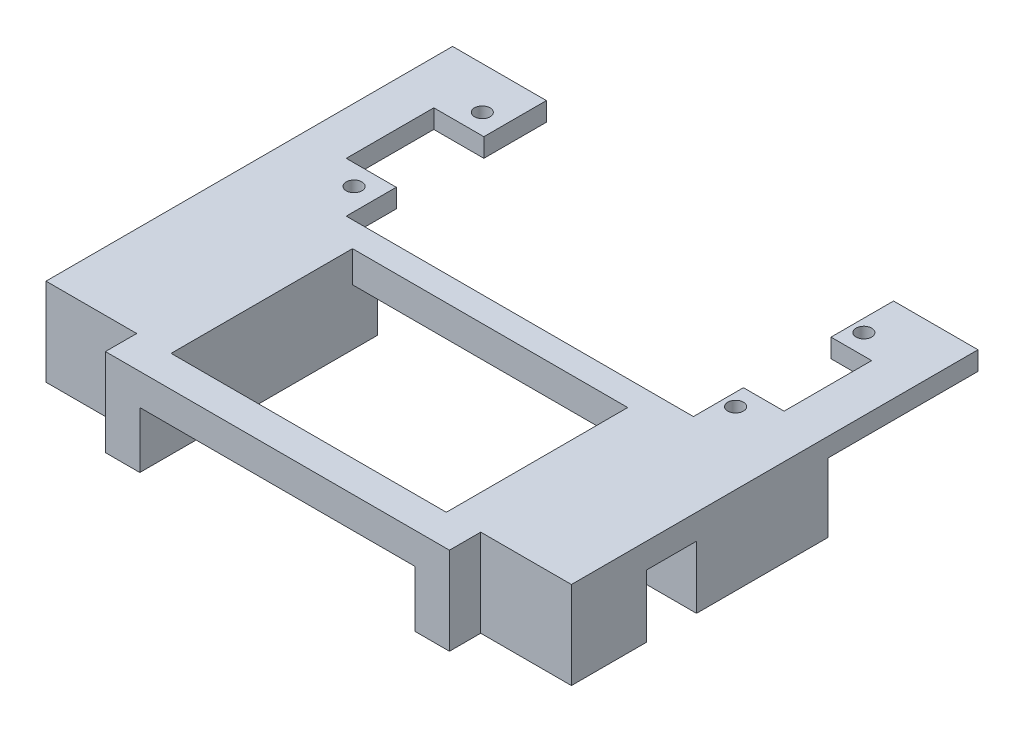
SolidWorks part; units mm, degrees
ref_plane "Front Plane" through (0, 0, 0) normal (0, 0, 1) x (1, 0, 0)
ref_plane "Top Plane" through (0, 0, 0) normal (0, 1, 0) x (1, 0, 0)
ref_plane "Right Plane" through (0, 0, 0) normal (1, 0, 0) x (0, 0, -1)
sketch "Sketch1" plane through (0, 0, 0) normal (0, 1, 0) x (1, 0, 0)
  line L0 (0, 0) -> (0, 31.2652) construction
  line L1 (-29.5, -11) -> (29.5, -11)
  line L5 (-42, -60) -> (42, -60) construction
  line L6 (65.83, -60) -> (108.3156, -60) construction
  line L8 (-42, -11) -> (42, -11)
  line L11 (-5.25, -11) -> (5.25, -11)
  line L13 (-35, -13) -> (35, -13)
  line L14 (-35, -13) -> (-35, -43)
  line L15 (-42, -76) -> (42, -76)
  line L16 (-115.1518, -60) -> (-65.222, -60) construction
  line L21 (42, -11) -> (42, -76)
  line L22 (-42, -11) -> (-42, -76)
  line L23 (-35, -43) -> (35, -43)
  line L28 (-22, -47) -> (22, -47)
  line L29 (-22, -47) -> (-22, -76)
  line L30 (-22, -76) -> (22, -76)
  line L31 (22, -47) -> (22, -76)
  line L32 (-22, -47) -> (22, -76) construction
  line L33 (-22, -76) -> (22, -47) construction
  line L34 (-27.5, -76) -> (27.5, -76)
  line L35 (-27.5, -76) -> (-27.5, -81)
  line L36 (-27.5, -81) -> (27.5, -81)
  line L37 (27.5, -76) -> (27.5, -81)
  line L38 (-27.5, -76) -> (27.5, -81) construction
  line L39 (-27.5, -81) -> (27.5, -76) construction
  line L40 (35, -13) -> (35, -43)
  line L41 (-35, -13) -> (35, -43) construction
  line L42 (-35, -43) -> (35, -13) construction
  point P9 (0, -28)
  point P13 (0, 0)
  point P20 (0, -11)
  point P30 (0, -78.5)
  point P40 (0, -61.5)
  dimension "D2" = 11
  dimension "D9" = 5
  dimension "D10" = 55
  dimension "D3" = 84
  dimension "D4" = 30
  dimension "D5" = 2
  dimension "D6" = 70
  dimension "D7" = 42
  dimension "D8" = 65
  dimension "D13" = 16
  dimension "D14" = 44
  dimension "D15" = 29
extrude "Boss-Extrude1" add sketch "Sketch1" along normal blind 5
sketch "Sketch2" plane through (0, 0, 0) normal (0, -1, 0) x (1, 0, 0)
  line L0 (0, 0) -> (0, 96.1896) construction
  line L1 (-42, 76) -> (-22, 76)
  line L2 (-42, 76) -> (-42, 43)
  line L3 (-42, 43) -> (-22, 43)
  line L4 (-22, 76) -> (-22, 43)
  line L5 (-42, 76) -> (-22, 43) construction
  line L6 (-42, 43) -> (-22, 76) construction
  line L7 (-42, 76) -> (-27.5, 76) construction
  line L8 (-42, 11) -> (-42, 76) construction
  line L9 (27.5, 76) -> (27.5, 81) construction
  line L10 (22, 76) -> (27.5, 76)
  line L11 (42, 43) -> (22, 43)
  line L12 (22, 76) -> (22, 43)
  line L13 (42, 76) -> (22, 76)
  line L14 (42, 76) -> (42, 43)
  line L15 (-35, 43) -> (35, 43) construction
  line L16 (-42, 11) -> (-42, 76) construction
  line L17 (-42, 43) -> (-35, 43)
  line L18 (-42, 43) -> (-42, 35)
  line L19 (-42, 35) -> (-35, 35)
  line L20 (-35, 43) -> (-35, 35)
  line L21 (-42, 43) -> (-35, 35) construction
  line L22 (-42, 35) -> (-35, 43) construction
  line L23 (42, 35) -> (35, 35)
  line L24 (-22, 47) -> (-22, 76) construction
  line L25 (22, 76) -> (22, 81)
  line L26 (22, 81) -> (27.5, 81)
  line L27 (27.5, 76) -> (27.5, 81)
  line L28 (22, 76) -> (27.5, 81) construction
  line L29 (22, 81) -> (27.5, 76) construction
  line L30 (-27.5, 81) -> (27.5, 81) construction
  line L31 (-22, 76) -> (22, 76) construction
  line L32 (-22, 81) -> (-27.5, 81)
  line L33 (-27.5, 76) -> (-27.5, 81)
  line L34 (-22, 76) -> (-27.5, 76)
  line L35 (-22, 76) -> (-22, 81)
  line L36 (35, 43) -> (35, 35)
  line L37 (42, 43) -> (35, 43)
  line L38 (42, 43) -> (42, 35)
  point P0 (-32, 59.5)
  point P21 (-38.5, 39)
  point P29 (24.75, 78.5)
  point P43 (0, 12)
  line M5 (42, 76) -> (27.5, 76)
  line M9 (-27.5, 76) -> (-42, 76)
  line M10 (-42, 76) -> (-42, 11)
  line M12 (42, 11) -> (42, 76)
  line M14 (-22, 47) -> (-22, 76)
  line M16 (22, 76) -> (22, 47)
  line M18 (-35, 13) -> (-35, 43)
  line M19 (-35, 43) -> (35, 43)
  dimension "D1" = 8
  dimension "D2" = 7
extrude "Boss-Extrude2" add sketch "Sketch2" along normal blind 9 contours L12 L11 L10 M16 M19 M12 M5 | L4 L1 L3 M14 M9 M10 M19 | L19 L3 M10 M18
sketch "Sketch3" plane through (0, 0, 0) normal (0, -1, 0) x (1, 0, 0)
  line L13 (-42, 35) -> (-42, 11)
  line L15 (42, 35) -> (35, 35)
  line L21 (-42, 35) -> (-42, 11)
  line L27 (-35, 13) -> (-35, 35)
  line L29 (-35, 13) -> (-35, 35)
  line L32 (35, 35) -> (35, 13)
  line L35 (35, 35) -> (35, 13)
  line L37 (-35, 35) -> (-42, 35)
  line L38 (-35, 35) -> (-42, 35)
  line L39 (35, 13) -> (-35, 13)
  line L40 (35, 13) -> (-35, 13)
  line L41 (-42, 11) -> (42, 11)
  line L42 (-42, 11) -> (42, 11)
  line L43 (42, 11) -> (42, 35)
  line L44 (42, 11) -> (42, 35)
  line L45 (42, 35) -> (35, 35)
  dimension "D1" = 0
extrude "Cut-Extrude1" cut sketch "Sketch3" against normal blind 2
sketch "Sketch4" plane through (0, 5, 0) normal (0, 1, 0) x (1, 0, 0)
  line L0 (0, 0) -> (0, -72.3692) construction
  line L1 (-42, -11) -> (42, -11) construction
  circle A0 centre (-28, -46) radius 1.65
  circle A2 centre (28, -46) radius 1.65
  dimension "D3" = 3.3
  dimension "D1" = 28
  dimension "D2" = 35
extrude "Cut-Extrude2" [suppressed] cut sketch "Sketch4" against normal up to surface (14 mm away)
sketch "Sketch5" [suppressed] plane through (0, 5, 0) normal (0, 1, 0) x (1, 0, 0)
  line L0 (0, 0) -> (0, 24.796) construction
  circle A0 centre (28, -46) radius 1.65 construction
  circle A1 centre (-28, -46) radius 1.65 construction
  circle A2 centre (28, -46) radius 1.65
  circle A3 centre (-28, -46) radius 1.65
  circle A4 centre (-28, -46) radius 2.75
  circle A5 centre (28, -46) radius 2.75
  dimension "D1" = 5.5
extrude "Cut-Extrude3" [suppressed] cut sketch "Sketch5" against normal blind 10
sketch "Sketch6" plane through (0, 5, 0) normal (0, 1, 0) x (1, 0, 0)
  line L0 (0, -28) -> (0, 0) construction
  line L1 (-30.5, -17.75) -> (30.5, -17.75)
  line L2 (-30.5, -17.75) -> (-30.5, -38.25)
  line L3 (-30.5, -38.25) -> (30.5, -38.25)
  line L4 (30.5, -17.75) -> (30.5, -38.25)
  line L5 (-30.5, -17.75) -> (30.5, -38.25) construction
  line L6 (-30.5, -38.25) -> (30.5, -17.75) construction
  line L7 (0, -28) -> (-35, -28) construction
  line L8 (-35, -13) -> (-35, -43) construction
  line L9 (27, -13) -> (27, -21)
  line L10 (-35, -13) -> (35, -13) construction
  line L11 (27, -21) -> (35, -21)
  line L12 (35, -13) -> (35, -43) construction
  line L14 (-27, -13) -> (-27, -21)
  line L15 (-27, -21) -> (-35, -21)
  line L16 (27, -43) -> (27, -35)
  line L17 (27, -35) -> (35, -35)
  line L18 (-27, -43) -> (-27, -35)
  line L19 (-27, -35) -> (-35, -35)
  line L20 (-35, -43) -> (35, -43) construction
  line L21 (-35, -13) -> (-35, -43)
  line L22 (-35, -13) -> (35, -13)
  line L23 (35, -13) -> (35, -43)
  line L24 (-35, -43) -> (35, -43)
  circle A0 centre (-30.5, -17.75) radius 1.25
  circle A1 centre (30.5, -17.75) radius 1.25
  circle A2 centre (30.5, -38.25) radius 1.25
  circle A3 centre (-30.5, -38.25) radius 1.25
  point P0 (0, -28)
  line M17 (-35, -13) -> (35, -13)
  line M18 (35, -13) -> (35, -43)
  line M19 (35, -43) -> (-35, -43)
  line M20 (-35, -43) -> (-35, -13)
  dimension "D3" = 2.5
  dimension "D1" = 10.25
  dimension "D2" = 30.5
  dimension "D4" = 8
  dimension "D5" = 8
extrude "Boss-Extrude3" add sketch "Sketch6" against normal blind 3 contours A0 L1 L14 L15 L2 M17 M20 | A0 L2 L15 L14 L1 | L3 A3 L2 L19 L18 M20 M19 | L2 A3 L3 L18 L19 | A2 L3 L16 L17 L4 M19 M18 | A2 L4 L17 L16 L3 | L1 A1 L4 L11 L9 M18 M17 | L4 A1 L1 L9 L11
sketch "Sketch7" plane through (0, 5, 0) normal (0, 1, 0) x (1, 0, 0)
  line L0 (-27, -13) -> (-27, -11)
  line L1 (-42, -11) -> (42, -11) construction
  line L2 (27, -13) -> (27, -11)
  line L3 (-27, -13) -> (27, -13) construction
  line L4 (-27, -13) -> (27, -13)
  line L5 (27, -13) -> (27, -21) construction
  line L6 (27, -13) -> (27, -21)
  line L7 (28.5, -11) -> (28.5, -21)
  line L8 (27, -21) -> (35, -21) construction
  line L9 (-42, -11) -> (42, -11)
  line L10 (27, -21) -> (35, -21)
  line L11 (27.5, -81) -> (27.5, -76)
  line L12 (27.5, -76) -> (42, -76)
  line L13 (42, -76) -> (42, -11)
  line L14 (42, -11) -> (-42, -11)
  line L15 (-42, -11) -> (-42, -76)
  line L16 (-42, -76) -> (-27.5, -76)
  line L17 (-27.5, -76) -> (-27.5, -81)
  line L18 (-27.5, -81) -> (27.5, -81)
  line L22 (27, -11) -> (-27, -11)
  line L27 (27, -35) -> (28.5, -35)
  line L28 (28.5, -35) -> (28.5, -43)
  line L29 (28.5, -43) -> (27, -43)
  line L30 (27, -43) -> (27, -35)
  line L31 (27, -35) -> (35, -35) construction
  line L32 (-27, -43) -> (27, -43) construction
  line M15 (-27, -13) -> (27, -13)
  line M16 (27, -13) -> (27, -21)
  line M17 (27, -21) -> (35, -21)
  line M24 (42, -11) -> (-42, -11)
  dimension "D2" = 1.5
  dimension "D1" = 0
extrude "Cut-Extrude4" cut sketch "Sketch7" against normal blind 10 contours L7 L2 M24 M16 M17 | L2 L0 M15 M24 | L30 L27 L28 L29
sketch "Sketch8" plane through (0, -9, 0) normal (0, -1, 0) x (1, 0, 0)
  line L0 (0, 0) -> (0, 72.1274) construction
  line L1 (-42, 64) -> (-32, 64)
  line L2 (-42, 64) -> (-42, 56)
  line L3 (-42, 56) -> (-32, 56)
  line L4 (-32, 64) -> (-32, 56)
  line L5 (-42, 64) -> (-32, 56) construction
  line L6 (-42, 56) -> (-32, 64) construction
  line L7 (-42, 76) -> (-42, 35) construction
  line L8 (-42, 76) -> (-27.5, 76) construction
  line L9 (42, 56) -> (32, 56)
  line L10 (32, 64) -> (32, 56)
  line L11 (42, 64) -> (32, 64)
  line L12 (42, 64) -> (42, 56)
  point P0 (-37, 60)
  dimension "D1" = 10
  dimension "D2" = 8
  dimension "D3" = 16
extrude "Cut-Extrude5" cut sketch "Sketch8" against normal blind 10
equation "\"10.005mmmm\"=10"
